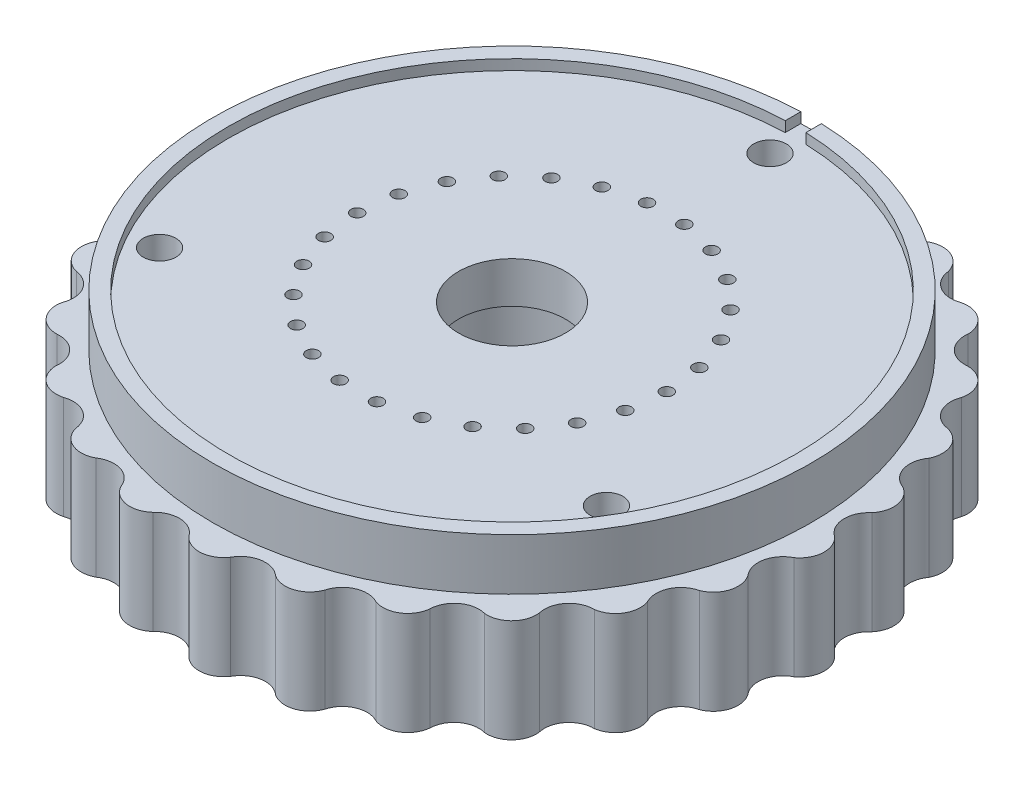
SolidWorks part; units mm, degrees
material "1060 Alloy"
ref_plane "Front Plane" through (0, 0, 0) normal (0, 0, 1) x (1, 0, 0)
ref_plane "Top Plane" through (0, 0, 0) normal (0, 1, 0) x (1, 0, 0)
ref_plane "Right Plane" through (0, 0, 0) normal (1, 0, 0) x (0, 0, -1)
sketch "Wheel" plane through (0, 0, 0) normal (0, 1, 0) x (1, 0, 0)
  line L0 (0, 0) -> (45.5848, 0) construction
  line L1 (0, 0) -> (41.8043, 10.3038) construction
  line L2 (0, 0) -> (29.1283, 7.1795)
  line L3 (0, 0) -> (30, 0)
  line L4 (0, 0) -> (42.9769, 5.2183) construction
  line L5 (29.1283, 7.1795) -> (30.3419, 7.4786)
  line L6 (30, 0) -> (31.25, 0)
  circle A0 centre (0, 0) radius 30 construction
  circle A1 centre (0, 0) radius 32.5 construction
  circle A2 centre (0, 0) radius 31.25 construction
  arc A3 (30.3419, 7.4786) -> (31.0877, 3.7747) centre (29.2636, 5.3345) cw
  arc A4 (31.0877, 3.7747) -> (31.25, 0) centre (0.4989, 0.5684) ccw construction
  arc A5 (31.0877, 3.7747) -> (31.25, 0) centre (32.6478, 1.951) ccw
  circle A6 centre (32.6478, 1.951) radius 2.4 construction
  dimension "D1" = 60
  dimension "D6" = 4.8
  dimension "D2" = 2.5
  dimension "D3" = 13.846
  dimension "D4" = 1.25
  dimension "D5" = 6.923
extrude "Extrude wheel" add sketch "Wheel" along normal blind 10
pattern_circular "CirPattern1" count 26 over 360 about axis through (0, 0, 0) along (0, 1, 0) of "Extrude wheel"
sketch "Sketch4" plane through (0, 10, 0) normal (0, 1, 0) x (1, 0, 0)
  circle A0 centre (0, 0) radius 29
  dimension "D1" = 58
extrude "Boss-Extrude1" add sketch "Sketch4" along normal blind 5
sketch "Bearing hole" plane through (0, 15, 0) normal (0, 1, 0) x (1, 0, 0)
  circle A0 centre (0, 0) radius 5.18
  dimension "D1" = 10.36
extrude "Cut bearing hole" cut sketch "Bearing hole" against normal through all
sketch "PCB inset" plane through (0, 15, 0) normal (0, 1, 0) x (1, 0, 0)
  line L0 (-1, 27.4818) -> (-1, 29.4818)
  line L1 (-1, 29.4818) -> (1, 29.4818)
  line L2 (1, 29.4818) -> (1, 27.4818)
  line L3 (0, 0) -> (0, 37.4364) construction
  arc A0 (-1, 27.4818) -> (1, 27.4818) centre (0, 0) ccw
  point P7 (0, 29.4818)
  dimension "D1" = 55
  dimension "D2" = 2
  dimension "D3" = 2
extrude "PCB inset cut" cut sketch "PCB inset" against normal blind 1
sketch "PCB inset 2" plane through (0, 0, 0) normal (0, -1, 0) x (1, 0, 0)
  line L0 (0, 0) -> (0, -38.2083) construction
  line L1 (1, -27.4818) -> (1, -29.4818)
  line L2 (1, -29.4818) -> (-1, -29.4818)
  line L3 (-1, -29.4818) -> (-1, -27.4818)
  arc A0 (1, -27.4818) -> (-1, -27.4818) centre (0, 0) ccw
  point P8 (0, -29.4818)
  dimension "D1" = 55
  dimension "D2" = 2
  dimension "D3" = 2
extrude "PCB inset cut 2" cut sketch "PCB inset 2" against normal blind 1
sketch "PCB output holes" plane through (0, 14, 0) normal (0, 1, 0) x (1, 0, 0)
  line L0 (0, 0) -> (60.8892, 0) construction
  line L1 (0, 0) -> (59.1575, 14.581) construction
  line L2 (0, 0) -> (60.8984, 0) construction
  circle A0 centre (15, 0) radius 0.6
  circle A1 centre (14.5641, -3.5897) radius 0.6
  circle A2 centre (13.2818, -6.9708) radius 0.6
  circle A3 centre (11.2277, -9.9468) radius 0.6
  circle A4 centre (8.521, -12.3448) radius 0.6
  circle A5 centre (5.3191, -14.0252) radius 0.6
  circle A6 centre (1.8081, -14.8906) radius 0.6
  circle A7 centre (-1.8081, -14.8906) radius 0.6
  circle A8 centre (-5.3191, -14.0252) radius 0.6
  circle A9 centre (-8.521, -12.3448) radius 0.6
  circle A10 centre (-11.2277, -9.9468) radius 0.6
  circle A11 centre (-13.2818, -6.9708) radius 0.6
  circle A12 centre (-14.5641, -3.5897) radius 0.6
  circle A13 centre (-15, 0) radius 0.6
  circle A14 centre (-14.5641, 3.5897) radius 0.6
  circle A15 centre (-13.2818, 6.9708) radius 0.6
  circle A16 centre (-11.2277, 9.9468) radius 0.6
  circle A17 centre (-8.521, 12.3448) radius 0.6
  circle A18 centre (-5.3191, 14.0252) radius 0.6
  circle A19 centre (-1.8081, 14.8906) radius 0.6
  circle A20 centre (1.8081, 14.8906) radius 0.6
  circle A21 centre (5.3191, 14.0252) radius 0.6
  circle A22 centre (8.521, 12.3448) radius 0.6
  circle A23 centre (11.2277, 9.9468) radius 0.6
  circle A24 centre (13.2818, 6.9708) radius 0.6
  circle A25 centre (14.5641, 3.5897) radius 0.6
  point P60 (0, 0)
  dimension "D5" = 1.2
  dimension "D1" = 13.846
  dimension "D2" = 0
  dimension "D3" = 15
  dimension "D4" = 26
extrude "PCB output holes cut" cut sketch "PCB output holes" against normal through all
sketch "Sketch5" plane through (0, 1, 0) normal (0, -1, 0) x (1, 0, 0)
  line L0 (0, 0) -> (0, -40.6677) construction
  circle A0 centre (0, -25) radius 1.5875
  circle A1 centre (-21.6506, 12.5) radius 1.5875
  circle A2 centre (21.6506, 12.5) radius 1.5875
  point P12 (0, 0)
  dimension "D1" = 3.175
  dimension "D2" = 25
  dimension "D3" = 3
extrude "Alignment pin cutout" cut sketch "Sketch5" against normal through all
sketch "Sketch6" [suppressed] plane through (0, 10, 0) normal (0, 1, 0) x (1, 0, 0)
  circle A0 centre (0, 0) radius 48.4873
extrude "Cut-Extrude1" [suppressed] cut sketch "Sketch6" along normal through all
sketch "Sketch7" plane through (0, 1, 0) normal (0, -1, 0) x (1, 0, 0)
  circle A0 centre (0, 0) radius 6.35
  dimension "D1" = 12.7
extrude "Cut-Extrude2" cut sketch "Sketch7" against normal up to surface (9 mm away) up to face at (0, 10, 0)
equation "\"Diameter\"=60"
equation "\"D1@Wheel\"=\"Diameter\""
equation "\"D5@Wheel\"=360/26/2"
equation "\"Bearing size\"= 10.36mm"
equation "\"D1@Bearing hole\"=\"Bearing size\""
equation "\"PCB diameter\"= 55mm"
equation "\"D1@PCB inset\"=\"PCB diameter\""
equation "\"D1@PCB inset 2\"=\"PCB diameter\""
